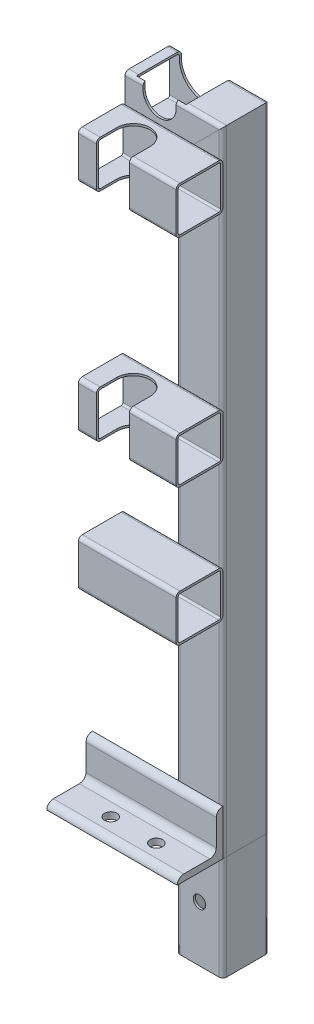
SolidWorks part; units mm, degrees
ref_plane "Front Plane" through (0, 0, 0) normal (0, 0, 1) x (1, 0, 0)
ref_plane "Top Plane" through (0, 0, 0) normal (0, 1, 0) x (1, 0, 0)
ref_plane "Right Plane" through (0, 0, 0) normal (1, 0, 0) x (0, 0, -1)
sketch "Sketch1" plane through (0, 0, 0) normal (0, 0, 1) x (1, 0, 0)
  line L0 (210.6, 0) -> (210.6, 468)
  line L1 (210.6, 468) -> (153.5, 468)
  line L2 (210.6, 0) -> (210.6, -80)
  dimension "D1" = 468
  dimension "D2" = 80
  dimension "D3" = 57.1
  dimension "D4" = 210.6
other "Structural MemberMain"
ref_plane "Plane1" through (210.6, 0, 0) normal (0, 1, 0) x (-1, 0, 0)
sketch "Sketch11" plane through (210.6, 0, 0) normal (0, 1, 0) x (-1, 0, 0)
  line L0 (-14.9, 16.3) -> (14.9, 16.3)
  line L1 (-14.9, 17.9) -> (14.9, 17.9)
  line L2 (-17.9, 14.9) -> (-17.9, -14.9)
  line L3 (-14.9, -17.9) -> (14.9, -17.9)
  line L4 (17.9, 14.9) -> (17.9, -14.9)
  line L5 (-17.9, 17.9) -> (17.9, -17.9) construction
  line L6 (-17.9, -17.9) -> (17.9, 17.9) construction
  line L7 (16.3, 14.9) -> (16.3, -14.9)
  line L8 (-14.9, -16.3) -> (14.9, -16.3)
  line L9 (-16.3, 14.9) -> (-16.3, -14.9)
  arc A0 (-17.9, -14.9) -> (-14.9, -17.9) centre (-14.9, -14.9) ccw
  arc A1 (14.9, -17.9) -> (17.9, -14.9) centre (14.9, -14.9) ccw
  arc A2 (17.9, 14.9) -> (14.9, 17.9) centre (14.9, 14.9) ccw
  arc A3 (-14.9, 17.9) -> (-17.9, 14.9) centre (-14.9, 14.9) ccw
  arc A4 (16.3, 14.9) -> (14.9, 16.3) centre (14.9, 14.9) ccw
  arc A5 (14.9, -16.3) -> (16.3, -14.9) centre (14.9, -14.9) ccw
  arc A6 (-16.3, -14.9) -> (-14.9, -16.3) centre (-14.9, -14.9) ccw
  arc A7 (-14.9, 16.3) -> (-16.3, 14.9) centre (-14.9, 14.9) ccw
  point P0 (0, 0)
  point P30 (0, 0)
  dimension "D3" = 3
  dimension "D1" = 35.8
  dimension "D2" = 35.8
  dimension "D4" = 1.6
sketch "Sketch12" plane through (0, 0, 0) normal (0, 0, 1) x (1, 0, 0)
  line L1 (180, 480.7) -> (180, 491.1) construction
  line L2 (167.3, 480.7) -> (167.3, 491.1)
  line L3 (192.7, 480.7) -> (192.7, 491.1)
  line L4 (210.6, 468) -> (153.5, 468) construction
  line L5 (153.5, 485.9) -> (228.5, 485.9) construction
  arc A0 (167.3, 480.7) -> (192.7, 480.7) centre (180, 480.7) ccw
  arc A1 (192.7, 491.1) -> (167.3, 491.1) centre (180, 491.1) ccw
  point P2 (180, 485.9)
  dimension "D1" = 25.4
  dimension "D2" = 180
extrude "Cut-ExtrudeTopRailGuide" cut sketch "Sketch12" against normal through all and the other way through all
sketch "Sketch13" plane through (0, 0, 0) normal (0, 1, 0) x (1, 0, 0)
  line L0 (128.5, -17.9) -> (228.5, -17.9)
  line L1 (192.7, -17.9) -> (225.5, -17.9) construction
  line L3 (228.5, 14.9) -> (228.5, -14.9) construction
  point P4 (178.5, -17.9)
  dimension "D1" = 100
other "Structural MemberAngle"
ref_plane "Plane2" through (128.5, 0, 17.9) normal (1, 0, 0) x (0, 1, 0)
sketch "Sketch14" plane through (128.5, 0, 17.9) normal (1, 0, 0) x (0, 1, 0)
  line L0 (0, 0) -> (0, 35)
  line L1 (0, 17.5) -> (5, 17.5) construction
  line L2 (5, 30) -> (5, 10)
  line L3 (10, 5) -> (30, 5)
  line L4 (17.5, 5) -> (17.5, 0) construction
  line L5 (35, 0) -> (0, 0)
  arc A0 (35, 0) -> (30, 5) centre (30, 0) ccw
  arc A1 (0, 35) -> (5, 30) centre (0, 30) cw
  arc A2 (10, 5) -> (5, 10) centre (10, 10) cw
  point P10 (17.5, 0)
  point P14 (0, 17.5)
  point P15 (5, 17.5)
  point P16 (17.5, 5)
  point P17 (5, 35)
  point P18 (35, 5)
  point P21 (0, 0)
  dimension "D2" = 5
  dimension "D3" = 35
  dimension "Radius_1" = 5
  dimension "D1" = 5
sketch "Sketch15" plane through (0, 0, 0) normal (0, 1, 0) x (1, 0, 0)
  line L0 (178.5, -17.9) -> (178.5, -52.9) construction
  line L1 (228.5, -52.9) -> (128.5, -52.9) construction
  line L2 (-65.8005, -37.9) -> (422.8005, -37.9) construction
  line L3 (128.5, -17.9) -> (228.5, -17.9) construction
  line L4 (0, 28.933) -> (0, -28.933) construction
  circle A0 centre (162.5, -37.9) radius 4.7625
  circle A1 centre (197.5, -37.9) radius 4.7625
  point P7 (178.5, -37.9)
  point P16 (0, 0)
  dimension "D2" = 9.525
  dimension "D1" = 20
  dimension "D3" = 197.5
  dimension "D4" = 35
extrude "Cut-ExtrudeMountingHoles" cut sketch "Sketch15" along normal through all
sketch "Sketch16" plane through (0, 0, 0) normal (0, 0, 1) x (1, 0, 0)
  line L4 (199.05, 480.7) -> (199.05, 491.1)
  line L5 (160.95, 491.1) -> (160.95, 480.7)
  line L6 (199.05, 480.7) -> (199.05, 491.1)
  line L7 (160.95, 491.1) -> (160.95, 480.7)
  arc A4 (160.95, 480.7) -> (199.05, 480.7) centre (180, 480.7) ccw
  arc A5 (199.05, 491.1) -> (160.95, 491.1) centre (180, 491.1) ccw
  arc A6 (160.95, 480.7) -> (199.05, 480.7) centre (180, 480.7) ccw
  arc A7 (199.05, 491.1) -> (160.95, 491.1) centre (180, 491.1) ccw
  dimension "D1" = 6.35
extrude "Cut-ExtrudeEnlargeRailGuide" cut sketch "Sketch16" against normal through all and the other way up to surface
sketch "Sketch17" plane through (0, 0, 17.9) normal (0, 0, 1) x (1, 0, 0)
  line L0 (228.5, 465.4) -> (153.5, 465.4)
  line L1 (228.5, 485.9) -> (228.5, 0) construction
  line L2 (153.5, 453.1) -> (153.5, 482.9) construction
  line L3 (228.5, 299.4) -> (153.5, 299.4)
  line L4 (228.5, 194.4) -> (153.5, 194.4)
  dimension "D1" = 194.4
  dimension "D2" = 299.4
  dimension "D3" = 465.4
other "Structural Member1"
ref_plane "Plane3" through (228.5, 465.4, 17.9) normal (-1, 0, 0) x (0, -1, 0)
sketch "Sketch19" plane through (228.5, 447.5, 35.8) normal (-1, 0, 0) x (0, -1, 0)
  line L0 (-14.9, 16.3) -> (14.9, 16.3)
  line L1 (-14.9, 17.9) -> (14.9, 17.9)
  line L2 (-17.9, 14.9) -> (-17.9, -14.9)
  line L3 (-14.9, -17.9) -> (14.9, -17.9)
  line L4 (17.9, 14.9) -> (17.9, -14.9)
  line L5 (-17.9, 17.9) -> (17.9, -17.9) construction
  line L6 (-17.9, -17.9) -> (17.9, 17.9) construction
  line L7 (16.3, 14.9) -> (16.3, -14.9)
  line L8 (-14.9, -16.3) -> (14.9, -16.3)
  line L9 (-16.3, 14.9) -> (-16.3, -14.9)
  arc A0 (-17.9, -14.9) -> (-14.9, -17.9) centre (-14.9, -14.9) ccw
  arc A1 (14.9, -17.9) -> (17.9, -14.9) centre (14.9, -14.9) ccw
  arc A2 (17.9, 14.9) -> (14.9, 17.9) centre (14.9, 14.9) ccw
  arc A3 (-14.9, 17.9) -> (-17.9, 14.9) centre (-14.9, 14.9) ccw
  arc A4 (16.3, 14.9) -> (14.9, 16.3) centre (14.9, 14.9) ccw
  arc A5 (14.9, -16.3) -> (16.3, -14.9) centre (14.9, -14.9) ccw
  arc A6 (-16.3, -14.9) -> (-14.9, -16.3) centre (-14.9, -14.9) ccw
  arc A7 (-14.9, 16.3) -> (-16.3, 14.9) centre (-14.9, 14.9) ccw
  point P0 (0, 0)
  point P30 (0, 0)
  dimension "D3" = 3
  dimension "D1" = 35.8
  dimension "D2" = 35.8
  dimension "D4" = 1.6
sketch "Sketch20" plane through (0, 465.4, 0) normal (0, 1, 0) x (1, 0, 0)
  line L0 (180, -69.5) -> (180, -37.9) construction
  line L1 (167.3, -69.5) -> (167.3, -37.9)
  line L2 (192.7, -69.5) -> (192.7, -37.9)
  line L3 (128.5, -17.9) -> (228.5, -17.9) construction
  line L4 (153.5, -53.7) -> (228.5, -53.7) construction
  arc A0 (167.3, -69.5) -> (192.7, -69.5) centre (180, -69.5) ccw
  arc A1 (192.7, -37.9) -> (167.3, -37.9) centre (180, -37.9) ccw
  point P2 (180, -53.7)
  dimension "D1" = 20
  dimension "D2" = 25.4
  dimension "D3" = 180
extrude "Cut-Extrude1" cut sketch "Sketch20" against normal through all
sketch "Sketch21" plane through (0, 0, 17.9) normal (0, 0, 1) x (1, 0, 0)
  line L0 (210.6, 0) -> (210.6, -80) construction
  line L1 (128.5, 0) -> (228.5, 0) construction
  circle A0 centre (210.6, -37.5) radius 4.7625
  dimension "D1" = 9.525
  dimension "D2" = 37.5
  dimension "D3" = 210.6
extrude "Cut-Extrude2" cut sketch "Sketch21" against normal through all
